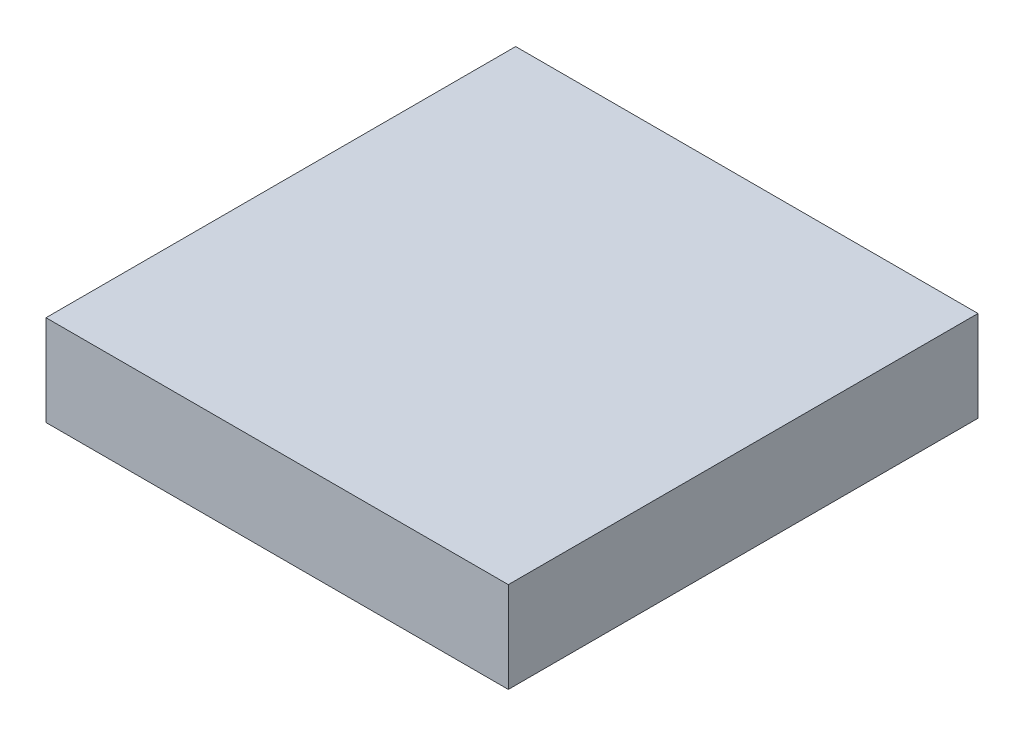
SolidWorks part; units mm, degrees
ref_plane "Front Plane" through (0, 0, 0) normal (0, 0, 1) x (1, 0, 0)
ref_plane "Top Plane" through (0, 0, 0) normal (0, 1, 0) x (1, 0, 0)
ref_plane "Right Plane" through (0, 0, 0) normal (1, 0, 0) x (0, 0, -1)
sketch "Sketch1" plane through (0, 0, 0) normal (0, 1, 0) x (1, 0, 0)
  line L1 (-27.5313, 27.7033) -> (60.5687, 27.7033)
  line L2 (-27.5313, 27.7033) -> (-27.5313, -61.7967)
  line L3 (-27.5313, -61.7967) -> (60.5688, -61.7967)
  line L4 (60.5687, 27.7033) -> (60.5688, -61.7967)
  dimension "D1" = 88.1
  dimension "D2" = 89.5
extrude "Boss-Extrude1" add sketch "Sketch1" along normal blind 17.3
